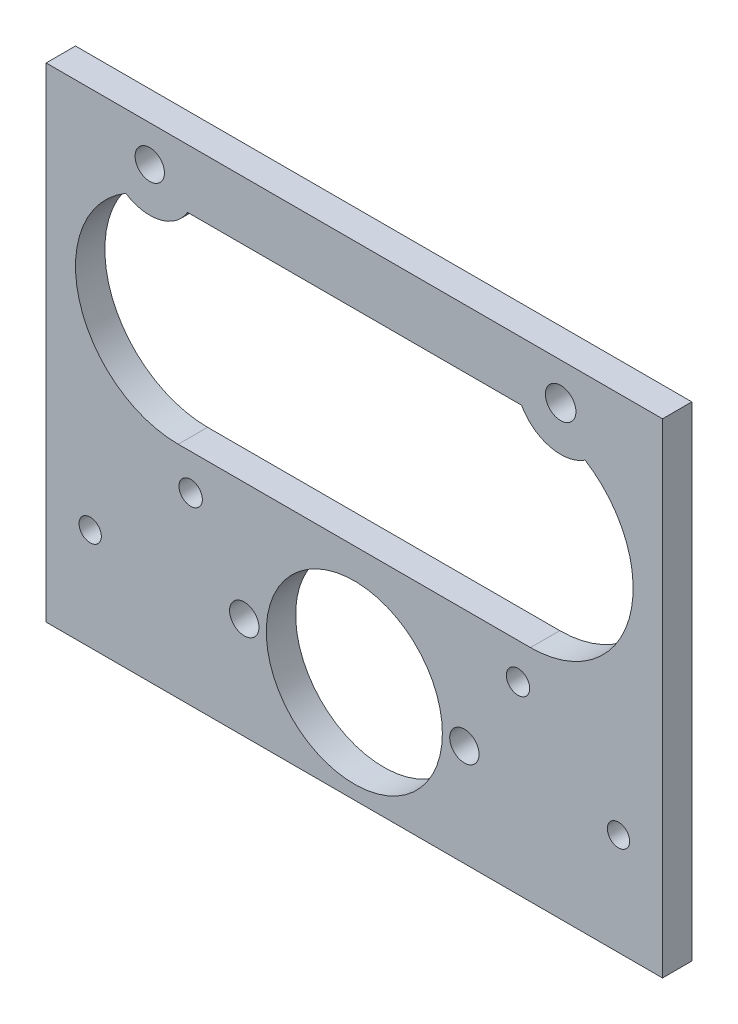
SolidWorks part; units mm, degrees
material "6061-T6 (SS)"
ref_plane "Front Plane" through (0, 0, 0) normal (0, 0, 1) x (1, 0, 0)
ref_plane "Top Plane" through (0, 0, 0) normal (0, 1, 0) x (1, 0, 0)
ref_plane "Right Plane" through (0, 0, 0) normal (1, 0, 0) x (0, 0, -1)
sketch "Sketch1" plane through (0, 0, 0) normal (0, 0, 1) x (1, 0, 0)
  line L0 (-66.675, 82.7405) -> (-66.675, -22.0345)
  line L1 (-66.675, -22.0345) -> (66.675, -22.0345)
  line L3 (-66.675, 82.7405) -> (66.675, 82.7405)
  line L4 (66.675, -22.0345) -> (66.675, 82.7405)
  line L5 (0, -22.0345) -> (0, 0) construction
  line L6 (-38.1, 47.8155) -> (38.1, 47.8155) construction
  line L7 (-36.0786, 70.0405) -> (36.185, 70.0405)
  line L8 (-38.1, 25.5905) -> (38.1, 25.5905)
  circle A7 centre (-57.15, 0) radius 2.413
  circle A8 centre (-35.4115, 17.8308) radius 2.5273
  circle A9 centre (-23.8125, 0) radius 3.175
  circle A10 centre (0, 0) radius 19.05
  circle A11 centre (23.8125, 0) radius 3.175
  circle A12 centre (35.4115, 17.8308) radius 2.5273
  circle A13 centre (57.15, 0) radius 2.413
  circle A14 centre (44.6415, 74.6933) radius 3.302 construction
  circle A15 centre (-44.2582, 74.9211) radius 3.175 construction
  circle A16 centre (44.6415, 74.6933) radius 3.302
  circle A17 centre (-44.2582, 74.9211) radius 3.175
  arc A18 (-49.4406, 66.9294) -> (-38.1, 25.5905) centre (-38.1, 47.8155) ccw
  arc A19 (38.1, 25.5905) -> (49.9388, 66.6249) centre (38.1, 47.8155) ccw
  arc A20 (-49.4406, 66.9294) -> (-36.0786, 70.0405) centre (-44.2582, 74.9211) ccw
  arc A21 (36.185, 70.0405) -> (49.9388, 66.6249) centre (44.6415, 74.6933) ccw
  circle A22 centre (-44.2582, 74.9211) radius 9.525 construction
  circle A23 centre (44.6415, 74.6933) radius 9.652 construction
  point P12 (0, 53.416)
  dimension "D5" = 22.225
  dimension "D1" = 133.35
  dimension "D2" = 104.775
  dimension "D3" = 22.0345
  dimension "D4" = 76.2
  dimension "D6" = 57.15
  dimension "D7" = 6.35
extrude "Boss-Extrude1" add sketch "Sketch1" against normal blind 6.35
